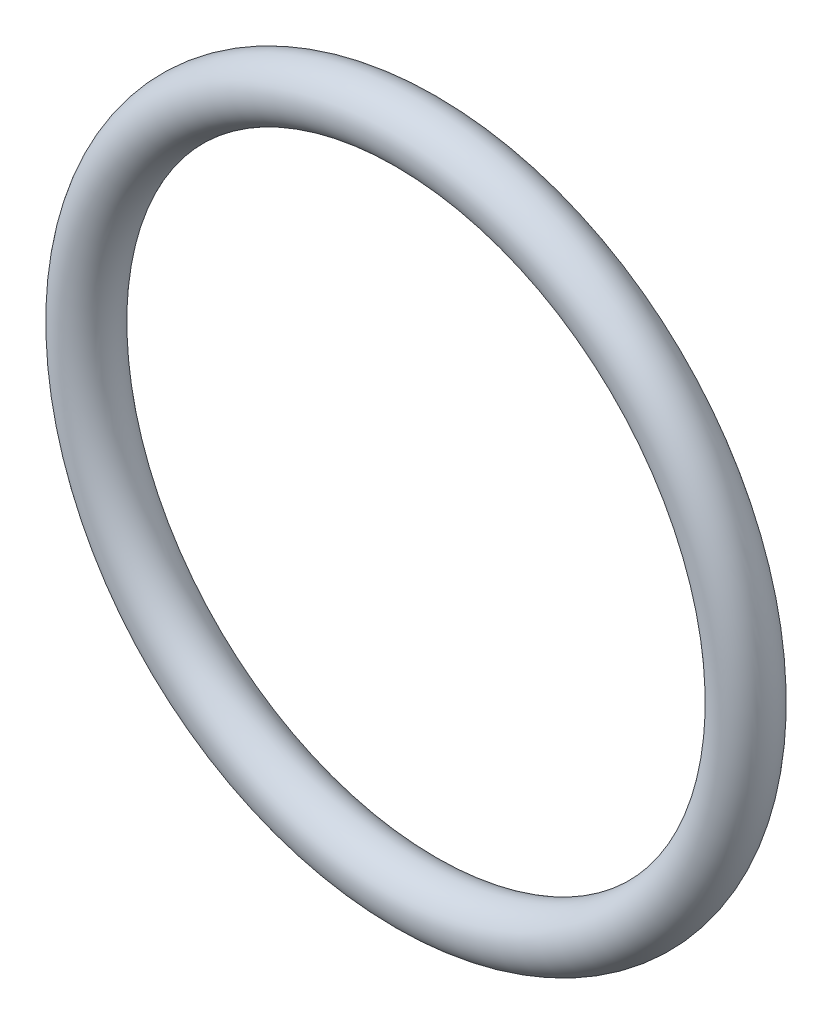
SolidWorks part; units mm, degrees
ref_plane "Plan de face" through (0, 0, 0) normal (0, 0, 1) x (1, 0, 0)
ref_plane "Plan de dessus" through (0, 0, 0) normal (0, 1, 0) x (1, 0, 0)
ref_plane "Plan de droite" through (0, 0, 0) normal (1, 0, 0) x (0, 0, -1)
sketch "Esquisse2" plane through (0, 0, 0) normal (0, 0, 1) x (1, 0, 0)
  circle A0 centre (0, 0) radius 23.0016
ref_plane "Plan1" through (0, 0, 0) normal (1, 0, 0) x (0, 0, -1)
sketch "Esquisse3" plane through (0, 0, 0) normal (1, 0, 0) x (0, 0, -1)
  circle A0 centre (0, 0) radius 23.0016
sketch "Esquisse4" plane through (0, 0, 0) normal (1, 0, 0) x (0, 0, -1)
  line L0 (0, 23.0016) -> (0, -23.0016) construction
  circle A0 centre (0, 23.0016) radius 2
  circle A1 centre (0, 0) radius 23.0016 construction
sweep "Balayage1" add profiles "Esquisse4" path "Esquisse2"
